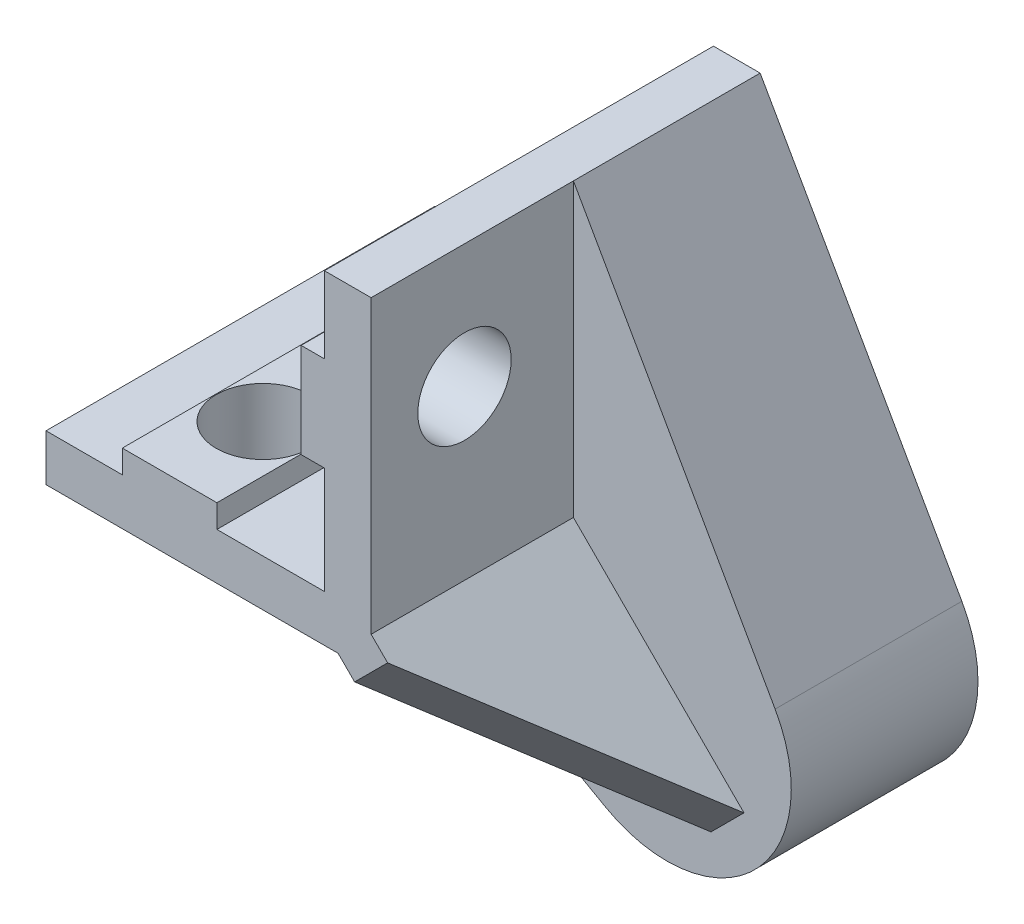
SolidWorks part; units mm, degrees
material "ABS"
ref_plane "Front Plane" through (0, 0, 0) normal (0, 0, 1) x (1, 0, 0)
ref_plane "Top Plane" through (0, 0, 0) normal (0, 1, 0) x (1, 0, 0)
ref_plane "Right Plane" through (0, 0, 0) normal (1, 0, 0) x (0, 0, -1)
sketch "Sketch1" plane through (0, 0, 0) normal (0, 0, 1) x (1, 0, 0)
  line L0 (227.0887, 62.283) -> (227.0887, 57.3796)
  line L1 (227.0887, 44.4296) -> (220.1787, 44.4296)
  line L2 (209.1953, 44.4296) -> (209.1953, 41.4296)
  line L3 (209.1953, 41.4296) -> (230.0887, 41.4296)
  line L4 (230.0887, 41.4296) -> (230.0887, 62.283)
  line L5 (230.0887, 62.283) -> (227.0887, 62.283)
  line L6 (214.0987, 45.9172) -> (214.0987, 44.4296)
  line L7 (220.1787, 45.9172) -> (220.1787, 44.4296)
  line L8 (220.1787, 45.9172) -> (214.0987, 45.9172)
  line L9 (225.5901, 57.3796) -> (227.0887, 57.3796)
  line L10 (225.5901, 51.2996) -> (227.0887, 51.2996)
  line L11 (225.5901, 51.2996) -> (225.5901, 57.3796)
  line L12 (227.0887, 51.2996) -> (227.0887, 44.4296)
  line L13 (214.0987, 44.4296) -> (209.1953, 44.4296)
  dimension "D1" = 17.8534
  dimension "D2" = 17.8934
  dimension "D3" = 1.4876
  dimension "D4" = 4.9034
  dimension "D5" = 4.9034
  dimension "D6" = 6.08
  dimension "D7" = 1.4986
  dimension "D8" = 3
extrude "Boss-Extrude1" add sketch "Sketch1" against normal blind 25
sketch3d "3DSketch1"
  line L0 (225.5901, 54.3396, 0) -> (230.0887, 54.3396, 0) construction
  line L1 (225.5901, 57.3796, 0) -> (225.5901, 51.2996, 0) construction
  line L2 (230.0887, 41.4296, 0) -> (230.0887, 62.283, 0) construction
  line L3 (230.0887, 54.3396, 0) -> (230.0887, 54.3396, -25) construction
  line L4 (230.0887, 41.4296, -25) -> (230.0887, 62.283, -25) construction
  line L5 (217.1387, 45.9172, 0) -> (217.1387, 41.4296, 0) construction
  line L6 (220.1787, 45.9172, 0) -> (214.0987, 45.9172, 0) construction
  line L7 (209.1953, 41.4296, 0) -> (230.0887, 41.4296, 0) construction
  line L8 (217.1387, 41.4296, 0) -> (217.1387, 41.4296, -25) construction
  line L9 (209.1953, 41.4296, -25) -> (230.0887, 41.4296, -25) construction
sketch "Sketch2" plane through (230.0887, 0, 0) normal (1, 0, 0) x (0, 0, -1)
  circle A0 centre (6, 54.3396) radius 3
  dimension "D1" = 6
  dimension "D2" = 6
extrude "Cut-Extrude1" cut sketch "Sketch2" against normal blind 15
sketch "Sketch3" plane through (0, 41.4296, 0) normal (0, -1, 0) x (1, 0, 0)
  circle A0 centre (217.1387, -6) radius 3
  dimension "D1" = 6
  dimension "D2" = 6
extrude "Cut-Extrude2" cut sketch "Sketch3" against normal blind 15
sketch "Sketch4" plane through (0, 0, -25) normal (0, 0, -1) x (-1, 0, 0)
  line L0 (-230.0887, 62.283) -> (-243.0517, 39.3686)
  line L1 (-230.0887, 62.283) -> (-227.0887, 62.283) construction
  line L2 (-232.1548, 28.4636) -> (-209.1953, 41.4296)
  line L3 (-209.1953, 41.4296) -> (-230.0887, 41.4296) construction
  line L4 (-209.1953, 44.4296) -> (-209.1953, 41.4296) construction
  line L5 (-209.1953, 41.4296) -> (-230.0887, 41.4296)
  line L6 (-230.0887, 41.4296) -> (-230.0887, 62.283)
  arc A0 (-243.0517, 39.3686) -> (-232.1548, 28.4636) centre (-236.0887, 35.4296) ccw
  dimension "D3" = 8
  dimension "D1" = 6
  dimension "D2" = 6
extrude "Boss-Extrude2" add sketch "Sketch4" against normal blind 12
ref_plane "Plane1" through (135.7174, 135.7666, 0) normal (-0.707, -0.7072, 0) x (0.7072, -0.707, 0)
sketch "Sketch5" plane through (135.7174, 135.7666, 0) normal (-0.707, -0.7072, 0) x (0.7072, -0.707, 0)
  line L1 (133.437, -13) -> (133.437, 0) construction
  line L2 (133.437, -13) -> (147.437, -13)
  line L3 (147.437, -13) -> (133.437, 0)
  line L4 (133.437, 0) -> (129.1944, 0)
  line L5 (129.1944, 0) -> (129.1944, -13)
  line L6 (129.1944, -13) -> (133.437, -13)
  dimension "D1" = 14
extrude "Boss-Extrude4" add sketch "Sketch5" along normal mid plane 3
sketch "Sketch6" plane through (0, 0, -25) normal (0, 0, -1) x (-1, 0, 0)
  circle A1 centre (-236.0887, 35.4296) radius 4.85
  arc A2 (-243.0517, 39.3686) -> (-232.1548, 28.4636) centre (-236.0887, 35.4296) ccw construction
  dimension "D1" = 9.7
extrude "Cut-Extrude3" cut sketch "Sketch6" against normal blind 9
